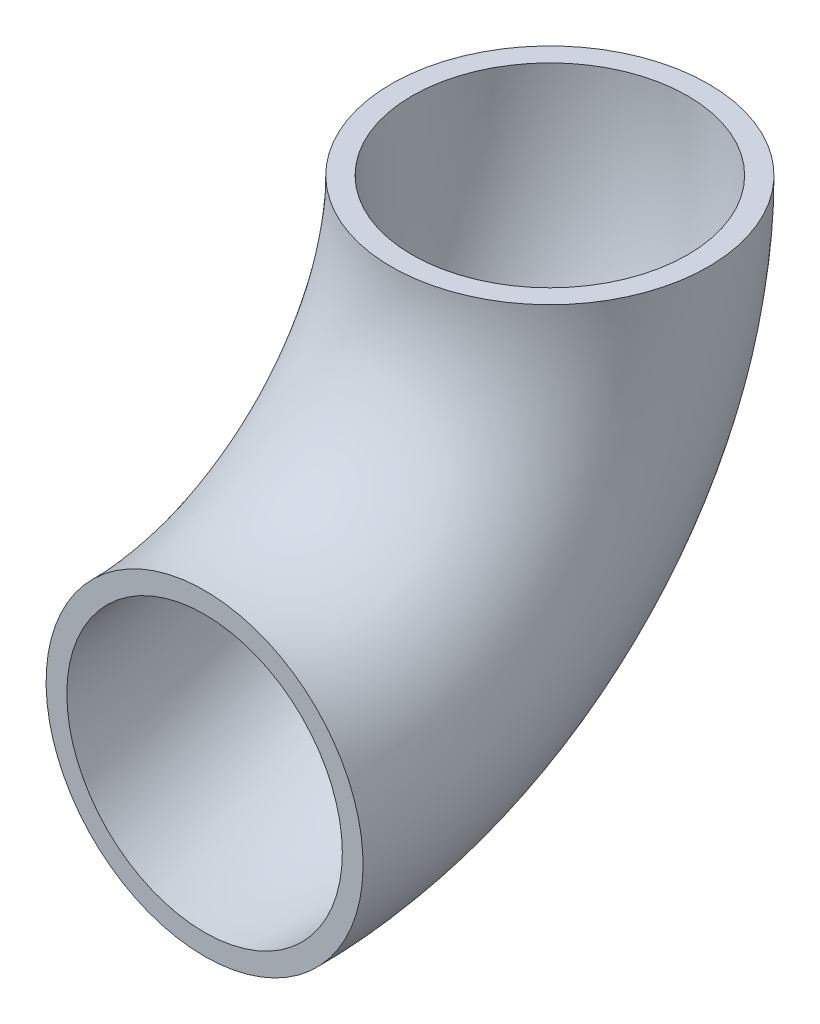
SolidWorks part; units mm, degrees
material "PVC Rigid"
ref_plane "Front Plane" through (0, 0, 0) normal (0, 0, 1) x (1, 0, 0)
ref_plane "Top Plane" through (0, 0, 0) normal (0, 1, 0) x (1, 0, 0)
ref_plane "Right Plane" through (0, 0, 0) normal (1, 0, 0) x (0, 0, -1)
sketch "Sketch1" plane through (0, 0, 0) normal (0, 0, 1) x (1, 0, 0)
  line L0 (-75.1382, 96.8375) -> (83.1045, 96.8375) construction
  circle A0 centre (0, 0) radius 38.6334
  circle A1 centre (0, 0) radius 44.45
  dimension "D1" = 88.9
  dimension "D2" = 77.2668
  dimension "D3" = 96.8375
revolve "Revolve1" add sketch "Sketch1" angle 90 about L0
